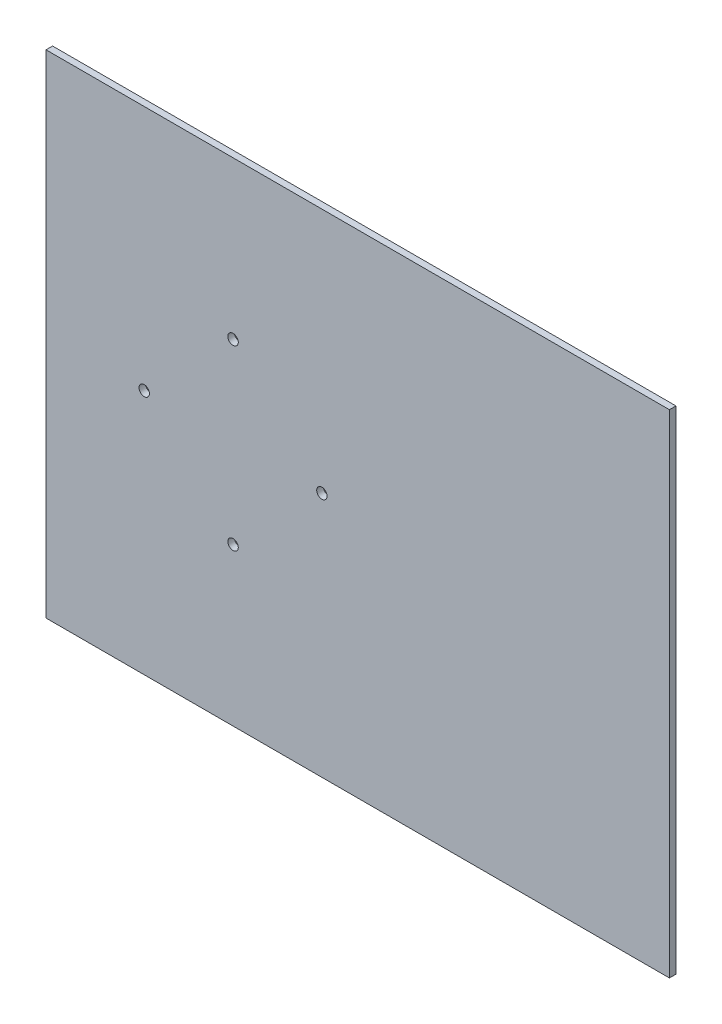
SolidWorks part; units mm, degrees
ref_plane "Front Plane" through (0, 0, 0) normal (0, 0, 1) x (1, 0, 0)
ref_plane "Top Plane" through (0, 0, 0) normal (0, 1, 0) x (1, 0, 0)
ref_plane "Right Plane" through (0, 0, 0) normal (1, 0, 0) x (0, 0, -1)
sketch "Sketch1" plane through (0, 0, 0) normal (0, 0, 1) x (1, 0, 0)
  line L1 (-112.6547, 52.9042) -> (267.3453, 52.9042)
  line L2 (-112.6547, 52.9042) -> (-112.6547, -247.0958)
  line L3 (-112.6547, -247.0958) -> (267.3453, -247.0958)
  line L4 (267.3453, 52.9042) -> (267.3453, -247.0958)
extrude "Boss-Extrude1" add sketch "Sketch1" along normal blind 4 contours L2 L3 L4 L1
sketch "Sketch7" plane through (0, 0, 4) normal (0, 0, 1) x (1, 0, 0)
  line L3 (1.3453, -97.0958) -> (1.3453, -46.0958) construction
  ellipse E0 centre (1.3453, -42.9458) end of major axis (4.5453, -42.9458) minor radius 3.15
  ellipse E1 centre (55.4953, -97.0958) end of major axis (55.4953, -100.2958) minor radius 3.15
  ellipse E2 centre (1.3453, -151.2458) end of major axis (-1.8547, -151.2458) minor radius 3.15
  ellipse E3 centre (-52.8047, -97.0958) end of major axis (-52.8047, -100.2958) minor radius 3.15
  dimension "D5" = 51
extrude "Cut-Extrude18" cut sketch "Sketch7" against normal blind 4
